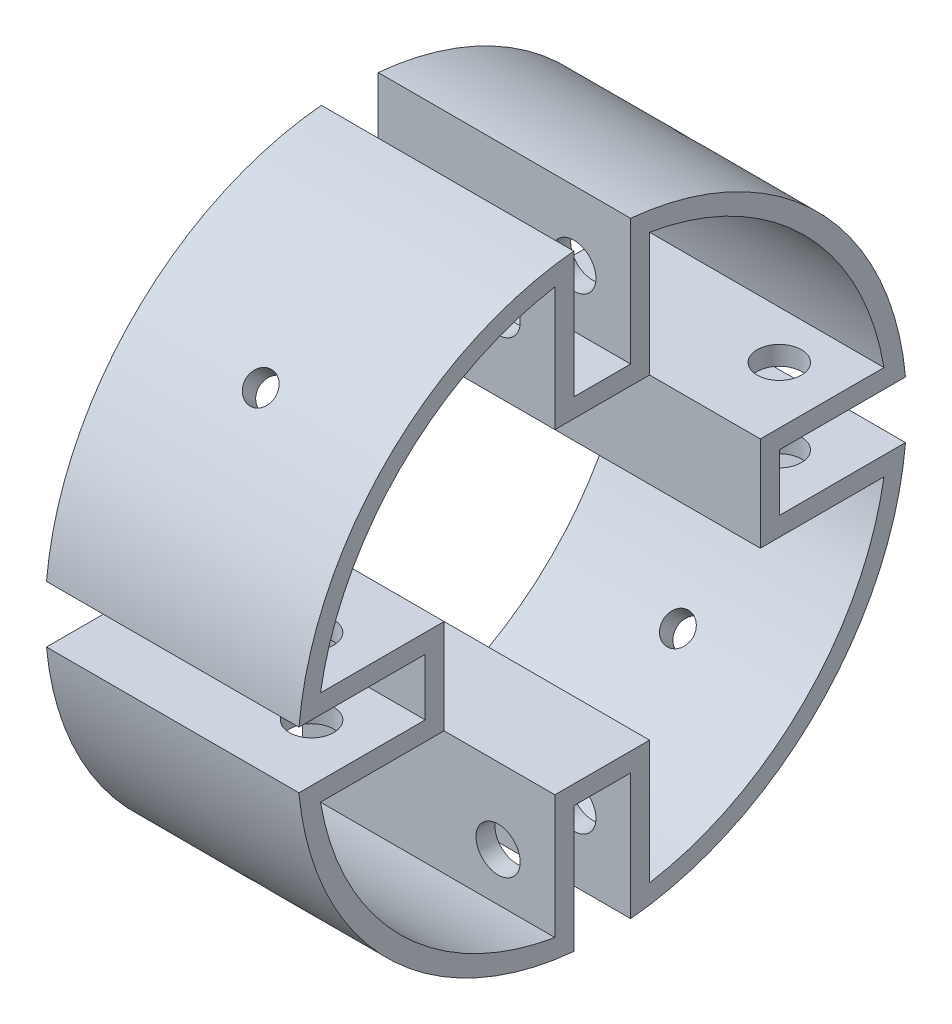
SolidWorks part; units mm, degrees
ref_plane "Front Plane" through (0, 0, 0) normal (0, 0, 1) x (1, 0, 0)
ref_plane "Top Plane" through (0, 0, 0) normal (0, 1, 0) x (1, 0, 0)
ref_plane "Right Plane" through (0, 0, 0) normal (1, 0, 0) x (0, 0, -1)
sketch "Sketch4" plane through (0, 0, 0) normal (1, 0, 0) x (0, 0, -1)
  circle A0 centre (0, 0) radius 48.26
  dimension "D1" = 96.52
extrude "Boss-Extrude2" add sketch "Sketch4" against normal blind 40
sketch "Sketch6" plane through (0, 0, 0) normal (1, 0, 0) x (0, 0, -1)
  line L0 (-4.5, 48.0497) -> (-4.5, 28.0497)
  line L1 (-4.5, 28.0497) -> (4.5, 28.0497)
  line L2 (4.5, 28.0497) -> (4.5, 48.0497)
  circle A1 centre (0, 0) radius 48.26
  circle A2 centre (0, 0) radius 48.26
  point P7 (0, 28.0497)
  circle M5 centre (0, 0) radius 48.26
  dimension "D2" = 20
  dimension "D3" = 9
  dimension "D1" = 0
extrude "Cut-Extrude1" cut sketch "Sketch6" against normal through all contours L1 L2 L0 M5
pattern_circular "CirPattern1" count 4 over 360 about axis through (0, 0, 0) along (1, 0, 0) of "Cut-Extrude1"
sketch "Sketch9" plane through (0, 0, 0) normal (1, 0, 0) x (0, 0, -1)
  line L0 (-25.0497, -7.5) -> (-44.6343, -7.5)
  line L1 (-7.5, -44.6343) -> (-7.5, -25.0497)
  line L2 (-7.5, -25.0497) -> (7.5, -25.0497)
  line L3 (7.5, -25.0497) -> (7.5, -44.6343)
  line L4 (44.6343, -7.5) -> (25.0497, -7.5)
  line L5 (25.0497, -7.5) -> (25.0497, 7.5)
  line L6 (25.0497, 7.5) -> (44.6343, 7.5)
  line L7 (7.5, 44.6343) -> (7.5, 25.0497)
  line L8 (7.5, 25.0497) -> (-7.5, 25.0497)
  line L9 (-7.5, 25.0497) -> (-7.5, 44.6343)
  line L10 (-44.6343, 7.5) -> (-25.0497, 7.5)
  line L11 (-25.0497, 7.5) -> (-25.0497, -7.5)
  line L24 (-28.0497, -4.5) -> (-48.0497, -4.5)
  line L25 (-28.0497, -4.5) -> (-48.0497, -4.5)
  line L26 (-4.5, -48.0497) -> (-4.5, -28.0497)
  line L27 (-4.5, -48.0497) -> (-4.5, -28.0497)
  line L28 (-4.5, -28.0497) -> (4.5, -28.0497)
  line L29 (-4.5, -28.0497) -> (4.5, -28.0497)
  line L30 (4.5, -28.0497) -> (4.5, -48.0497)
  line L31 (4.5, 48.0497) -> (4.5, 28.0497)
  line L32 (4.5, 28.0497) -> (-4.5, 28.0497)
  line L33 (-4.5, 28.0497) -> (-4.5, 48.0497)
  line L34 (4.5, -28.0497) -> (4.5, -48.0497)
  line L35 (48.0497, -4.5) -> (28.0497, -4.5)
  line L43 (4.5, 48.0497) -> (4.5, 28.0497)
  line L44 (4.5, 28.0497) -> (-4.5, 28.0497)
  line L45 (-4.5, 28.0497) -> (-4.5, 48.0497)
  line L57 (48.0497, -4.5) -> (28.0497, -4.5)
  line L58 (28.0497, -4.5) -> (28.0497, 4.5)
  line L59 (28.0497, -4.5) -> (28.0497, 4.5)
  line L60 (28.0497, 4.5) -> (48.0497, 4.5)
  line L61 (28.0497, 4.5) -> (48.0497, 4.5)
  line L62 (-48.0497, 4.5) -> (-28.0497, 4.5)
  line L63 (-48.0497, 4.5) -> (-28.0497, 4.5)
  line L64 (-28.0497, 4.5) -> (-28.0497, -4.5)
  line L65 (-28.0497, 4.5) -> (-28.0497, -4.5)
  arc A0 (-44.6343, -7.5) -> (-7.5, -44.6343) centre (0, 0) ccw
  arc A1 (7.5, -44.6343) -> (44.6343, -7.5) centre (0, 0) ccw
  arc A2 (44.6343, 7.5) -> (7.5, 44.6343) centre (0, 0) ccw
  arc A3 (-7.5, 44.6343) -> (-44.6343, 7.5) centre (0, 0) ccw
  arc A8 (-48.0497, -4.5) -> (-4.5, -48.0497) centre (0, 0) ccw
  arc A9 (4.5, -48.0497) -> (48.0497, -4.5) centre (0, 0) ccw
  arc A10 (4.5, -48.0497) -> (48.0497, -4.5) centre (0, 0) ccw
  arc A11 (48.0497, 4.5) -> (4.5, 48.0497) centre (0, 0) ccw
  arc A12 (-48.0497, -4.5) -> (-4.5, -48.0497) centre (0, 0) ccw
  arc A19 (48.0497, 4.5) -> (4.5, 48.0497) centre (0, 0) ccw
  arc A20 (-4.5, 48.0497) -> (-48.0497, 4.5) centre (0, 0) ccw
  arc A21 (-4.5, 48.0497) -> (-48.0497, 4.5) centre (0, 0) ccw
  dimension "D1" = 0
  dimension "D2" = 3
extrude "Cut-Extrude2" cut sketch "Sketch9" against normal up to surface (40 mm away) up to face at (-40, 0, 0)
sketch "Sketch7" plane through (0, 0, -4.5) normal (0, 0, 1) x (1, 0, 0)
  line L4 (0, 28.0497) -> (0, 48.0497)
  line L5 (0, 48.0497) -> (-40, 48.0497)
  line L6 (-40, 48.0497) -> (-40, 28.0497)
  line L7 (-40, 28.0497) -> (0, 28.0497)
  line L8 (0, 28.0497) -> (0, 48.0497)
  line L9 (0, 48.0497) -> (-40, 48.0497)
  line L10 (-40, 48.0497) -> (-40, 28.0497)
  line L11 (-40, 28.0497) -> (0, 28.0497)
  circle A0 centre (-9, 37.0497) radius 3.5
  dimension "D2" = 7
  dimension "D3" = 11
  dimension "D4" = 9
  dimension "D1" = 0
sketch "Sketch8" plane through (0, 4.5, 0) normal (0, -1, 0) x (1, 0, 0)
  line L4 (0, 28.0497) -> (0, 48.0497)
  line L5 (0, 48.0497) -> (-40, 48.0497)
  line L6 (-40, 48.0497) -> (-40, 28.0497)
  line L7 (-40, 28.0497) -> (0, 28.0497)
  line L8 (0, 28.0497) -> (0, 48.0497)
  line L9 (0, 48.0497) -> (-40, 48.0497)
  line L10 (-40, 48.0497) -> (-40, 28.0497)
  line L11 (-40, 28.0497) -> (0, 28.0497)
  circle A0 centre (-9, 37.0497) radius 3.5
  dimension "D1" = 7
  dimension "D3" = 11
  dimension "D4" = 9
  dimension "D2" = 0
extrude "Cut-Extrude3" cut sketch "Sketch7" along normal up to surface (15 mm away) from surface at -3 contours A0 up to face at (-20, 34.842, 7.5) starting at face at (-20, 34.842, -7.5)
extrude "Cut-Extrude4" cut sketch "Sketch8" along normal up to surface (15 mm away) from surface at -3 contours A0 up to face at (-20, -7.5, 34.842) starting at face at (-20, 7.5, 34.842)
mirror "Mirror1" about plane through (0, 0, 0) normal (0, 1, 0) of "Cut-Extrude3"
mirror "Mirror2" about plane through (0, 0, 0) normal (0, 0, 1) of "Cut-Extrude4"
ref_plane "Plane1" through (0, -34.125, 34.125) normal (0, -0.7071, 0.7071) x (1, 0, 0)
sketch "Sketch11" plane through (0, -34.125, 34.125) normal (0, -0.7071, 0.7071) x (1, 0, 0)
  line L0 (0, 0) -> (-40, 0) construction
  line L1 (-40, 30.7943) -> (-40, -30.7943) construction
  line L2 (-20, 30.7943) -> (-20, -30.7943) construction
  line L3 (-40, 30.7943) -> (0, 30.7943) construction
  line L4 (-40, -30.7943) -> (0, -30.7943) construction
  circle A0 centre (-20, 0) radius 2.3812
  point P11 (-20, 0)
  dimension "D1" = 4.7625
extrude "Cut-Extrude5" cut sketch "Sketch11" against normal up to next contours A0
ref_plane "Plane2" through (0, 0, 0) normal (0, 0.7071, -0.7071) x (-1, 0, 0)
mirror "Mirror3" about plane through (0, 0, 0) normal (0, 0.7071, -0.7071) of "Cut-Extrude5"
ref_plane "Plane3" through (0, 0, 0) normal (0, 0.7071, 0.7071) x (1, 0, 0)
sketch "Sketch13" plane through (0, 0, 0) normal (0, 0.7071, 0.7071) x (1, 0, 0)
  line L0 (-40, 0) -> (0, 0) construction
  line L1 (-40, 30.7943) -> (-40, -30.7943) construction
  line L2 (0, -30.7943) -> (0, 30.7943) construction
  circle A0 centre (-20, 0) radius 2.3812
  dimension "D1" = 4.7625
extrude "Cut-Extrude6" cut sketch "Sketch13" against normal through all both and the other way through all
